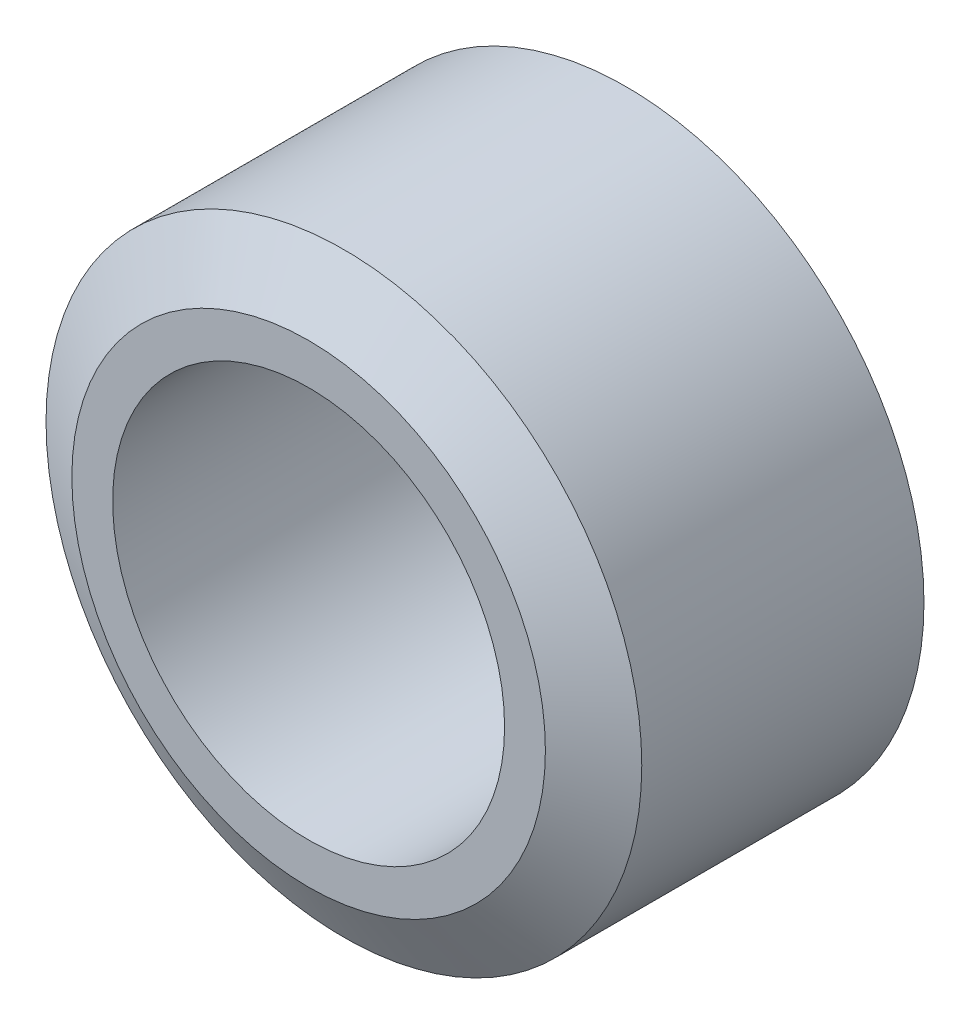
SolidWorks part; units mm, degrees
ref_plane "Plan de face" through (0, 0, 0) normal (0, 0, 1) x (1, 0, 0)
ref_plane "Plan de dessus" through (0, 0, 0) normal (0, 1, 0) x (1, 0, 0)
ref_plane "Plan de droite" through (0, 0, 0) normal (1, 0, 0) x (0, 0, -1)
sketch "Esquisse1" plane through (0, 0, 0) normal (0, 0, 1) x (1, 0, 0)
  circle A0 centre (0, 0) radius 7.6
  circle A1 centre (0, 0) radius 5
  dimension "D1" = 10
  dimension "D2" = 15.2
extrude "Boss.-Extru.1" add sketch "Esquisse1" along normal blind 9
chamfer "Chanfrein5" distance 0.9 angle 60 1 edges at (7.6, 0, 9)
chamfer "Chanfrein9" distance 0.9 angle 60 1 edges at (7.6, 0, 0)
